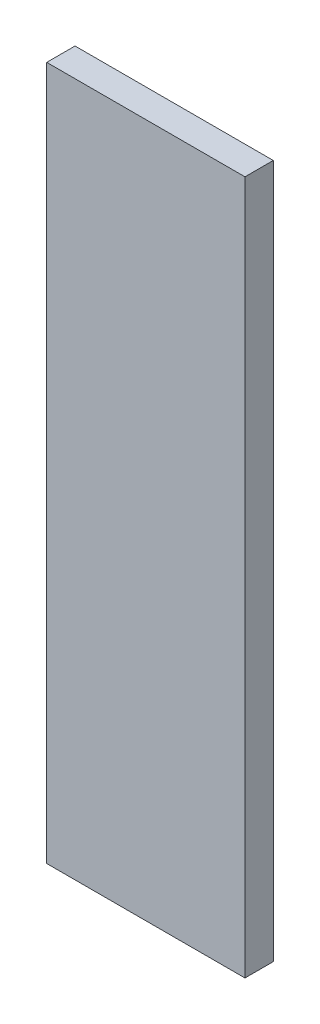
SolidWorks part; units mm, degrees
ref_plane "Plan de face" through (0, 0, 0) normal (0, 0, 1) x (1, 0, 0)
ref_plane "Plan de dessus" through (0, 0, 0) normal (0, 1, 0) x (1, 0, 0)
ref_plane "Plan de droite" through (0, 0, 0) normal (1, 0, 0) x (0, 0, -1)
sketch "Esquisse1" plane through (0, 0, 0) normal (0, 0, 1) x (1, 0, 0)
  line L1 (-41.0171, 16.9167) -> (28.9829, 16.9167)
  line L2 (-41.0171, 16.9167) -> (-41.0171, -228.0833)
  line L3 (-41.0171, -228.0833) -> (28.9829, -228.0833)
  line L4 (28.9829, 16.9167) -> (28.9829, -228.0833)
  dimension "D1" = 70
  dimension "D2" = 245
extrude "Boss.-Extru.1" add sketch "Esquisse1" along normal blind 10
